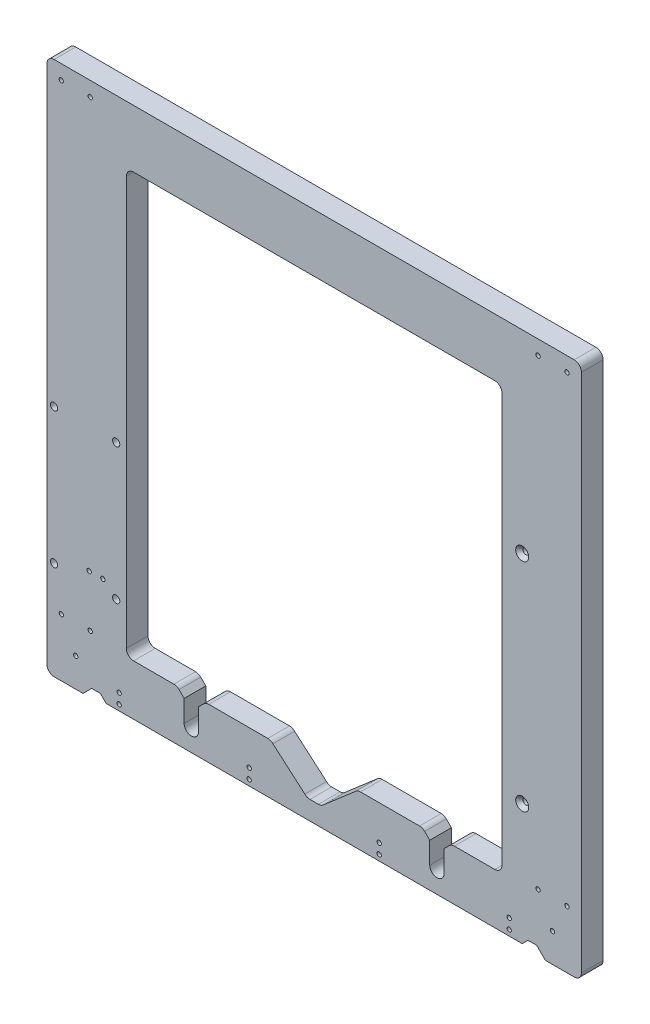
SolidWorks part; units mm, degrees
ref_plane "Plano frontal" through (0, 0, 0) normal (0, 0, 1) x (1, 0, 0)
ref_plane "Plano superior" through (0, 0, 0) normal (0, 1, 0) x (1, 0, 0)
ref_plane "Plano direito" through (0, 0, 0) normal (1, 0, 0) x (0, 0, -1)
sketch "Model" plane through (0, 0, 0) normal (0, 0, 1) x (1, 0, 0)
  line L0 (45.9594, 55.5362) -> (45.9594, 415.5362)
  line L1 (50.9594, 420.5362) -> (410.9594, 420.5362)
  line L2 (415.9594, 415.5362) -> (415.9594, 55.5362)
  line L3 (410.9594, 50.5362) -> (390.9594, 50.5362)
  line L4 (390.9594, 50.5362) -> (388.9594, 52.5362)
  line L5 (374.9594, 52.5362) -> (86.9594, 52.5362)
  line L6 (72.9594, 52.5362) -> (70.9594, 50.5362)
  line L7 (70.9594, 50.5362) -> (50.9594, 50.5362)
  line L8 (140.9594, 67.5362) -> (140.9594, 82.5362)
  line L9 (140.9594, 82.5362) -> (137.4239, 86.0718)
  line L10 (198.8884, 87.5362) -> (158.0305, 87.5362)
  line L11 (133.8884, 87.5362) -> (105.9594, 87.5362)
  line L12 (100.9594, 92.5362) -> (100.9594, 375.5362)
  line L13 (105.9594, 380.5362) -> (355.9594, 380.5362)
  line L14 (360.9594, 375.5362) -> (360.9594, 92.5362)
  line L15 (150.9594, 67.5362) -> (150.9594, 82.5362)
  line L16 (150.9594, 82.5362) -> (154.495, 86.0718)
  line L17 (320.9594, 82.5362) -> (320.9594, 67.5362)
  line L18 (310.9594, 67.5362) -> (310.9594, 82.5362)
  line L19 (310.9594, 82.5362) -> (307.4239, 86.0718)
  line L20 (228.0305, 65.5362) -> (233.8884, 65.5362)
  line L21 (237.4239, 67.0007) -> (259.495, 86.0718)
  line L22 (224.495, 67.0007) -> (202.4239, 86.0718)
  line L23 (263.0305, 87.5362) -> (303.8884, 87.5362)
  line L24 (388.9594, 52.5362) -> (384.9594, 56.5362)
  line L25 (384.9594, 56.5362) -> (378.9594, 56.5362)
  line L26 (378.9594, 56.5362) -> (374.9594, 52.5362)
  line L27 (72.9594, 52.5362) -> (76.9594, 56.5362)
  line L28 (76.9594, 56.5362) -> (82.9594, 56.5362)
  line L29 (82.9594, 56.5362) -> (86.9594, 52.5362)
  line L30 (328.0305, 87.5362) -> (355.9594, 87.5362)
  line L31 (320.9594, 82.5362) -> (324.495, 86.0718)
  arc A0 (140.9594, 67.5362) -> (150.9594, 67.5362) centre (145.9594, 67.5362) ccw
  arc A1 (310.9594, 67.5362) -> (320.9594, 67.5362) centre (315.9594, 67.5362) ccw
  circle A2 centre (95.9594, 56.5362) radius 1.5
  circle A3 centre (365.9594, 56.5362) radius 1.5
  circle A4 centre (275.9594, 56.5362) radius 1.5
  circle A5 centre (185.9594, 56.5362) radius 1.5
  circle A6 centre (55.9594, 90.5362) radius 1.5
  circle A7 centre (75.9594, 90.5362) radius 1.5
  circle A8 centre (65.9594, 70.5362) radius 1.5
  circle A9 centre (395.9594, 70.5362) radius 1.5
  circle A10 centre (385.9594, 90.5362) radius 1.5
  circle A11 centre (405.9594, 90.5362) radius 1.5
  circle A12 centre (405.9594, 410.5362) radius 1.5
  circle A13 centre (385.9594, 410.5362) radius 1.5
  circle A14 centre (55.9594, 410.5362) radius 1.5
  circle A15 centre (75.9594, 410.5362) radius 1.5
  circle A16 centre (93.911, 118.5016) radius 1.5
  circle A17 centre (50.911, 212.5016) radius 1.5
  circle A18 centre (93.911, 212.5016) radius 1.5
  circle A19 centre (50.8762, 118.5278) radius 1.5
  circle A20 centre (95.9594, 63.5362) radius 1.5
  circle A21 centre (365.9594, 63.5362) radius 1.5
  circle A22 centre (275.9594, 63.5362) radius 1.5
  circle A23 centre (185.9594, 63.5362) radius 1.5
  circle A24 centre (390.4594, 301.5362) radius 1.5 construction
  circle A25 centre (369.4594, 301.5362) radius 1.5 construction
  circle A26 centre (84.7094, 126.0362) radius 1.5
  circle A27 centre (75.2094, 126.0362) radius 1.5
  arc A28 (415.9594, 415.5362) -> (410.9594, 420.5362) centre (410.9594, 415.5362) ccw
  arc A29 (50.9594, 420.5362) -> (45.9594, 415.5362) centre (50.9594, 415.5362) ccw
  arc A30 (410.9594, 50.5362) -> (415.9594, 55.5362) centre (410.9594, 55.5362) ccw
  arc A31 (45.9594, 55.5362) -> (50.9594, 50.5362) centre (50.9594, 55.5362) ccw
  arc A32 (105.9594, 380.5362) -> (100.9594, 375.5362) centre (105.9594, 375.5362) ccw
  arc A33 (360.9594, 375.5362) -> (355.9594, 380.5362) centre (355.9594, 375.5362) ccw
  arc A34 (355.9594, 87.5362) -> (360.9594, 92.5362) centre (355.9594, 92.5362) ccw
  arc A35 (100.9594, 92.5362) -> (105.9594, 87.5362) centre (105.9594, 92.5362) ccw
  arc A36 (202.4239, 86.0718) -> (198.8884, 87.5362) centre (198.8884, 82.5362) ccw
  arc A37 (263.0305, 87.5362) -> (259.495, 86.0718) centre (263.0305, 82.5362) ccw
  arc A38 (233.8884, 65.5362) -> (237.4239, 67.0007) centre (233.8884, 70.5362) ccw
  arc A39 (224.495, 67.0007) -> (228.0305, 65.5362) centre (228.0305, 70.5362) ccw
  arc A40 (137.4239, 86.0718) -> (133.8884, 87.5362) centre (133.8884, 82.5362) ccw
  arc A41 (158.0305, 87.5362) -> (154.495, 86.0718) centre (158.0305, 82.5362) ccw
  arc A42 (307.4239, 86.0718) -> (303.8884, 87.5362) centre (303.8884, 82.5362) ccw
  arc A43 (328.0305, 87.5362) -> (324.495, 86.0718) centre (328.0305, 82.5362) ccw
  circle A44 centre (377.4594, 301.5362) radius 1.5 construction
  circle A45 centre (374.9594, 136.4362) radius 2 construction
  circle A46 centre (374.9594, 286.4362) radius 2 construction
  circle A47 centre (374.9594, 136.4362) radius 2
  circle A48 centre (374.9594, 286.4362) radius 2
extrude "Ressalto-extrusão1" add sketch "Model" along normal blind 15
sketch "Esboço1" plane through (0, 0, 0) normal (0, 0, -1) x (-1, 0, 0)
  circle A0 centre (-385.9594, 90.5362) radius 2.5
  circle A1 centre (-405.9594, 90.5362) radius 2.5
  circle A2 centre (-395.9594, 70.5362) radius 2.5
  circle A3 centre (-75.9594, 90.5362) radius 2.5
  circle A4 centre (-55.9594, 90.5362) radius 2.5
  circle A5 centre (-65.9594, 70.5362) radius 2.5
  circle A6 centre (-405.9594, 410.5362) radius 2.5
  circle A7 centre (-385.9594, 410.5362) radius 2.5
  circle A8 centre (-75.9594, 410.5362) radius 2.5
  circle A9 centre (-55.9594, 410.5362) radius 2.5
  circle A10 centre (-84.7094, 126.0362) radius 2.5
  circle A11 centre (-75.2094, 126.0362) radius 2.5
  dimension "D1" = 5
extrude "Corte-extrusão1" cut sketch "Esboço1" against normal blind 10
sketch "Esboço2" plane through (0, 0, 15) normal (0, 0, 1) x (1, 0, 0)
  circle A0 centre (50.911, 212.5016) radius 2.5
  circle A1 centre (93.911, 212.5016) radius 2.5
  circle A2 centre (93.911, 118.5016) radius 2.5
  circle A3 centre (50.8762, 118.5278) radius 2.5
  dimension "D1" = 5
extrude "Corte-extrusão2" cut sketch "Esboço2" against normal blind 10
chamfer "Chanfro1" distance 2.5 angle 45 1 edges at (376.9594, 286.4362, 15)
